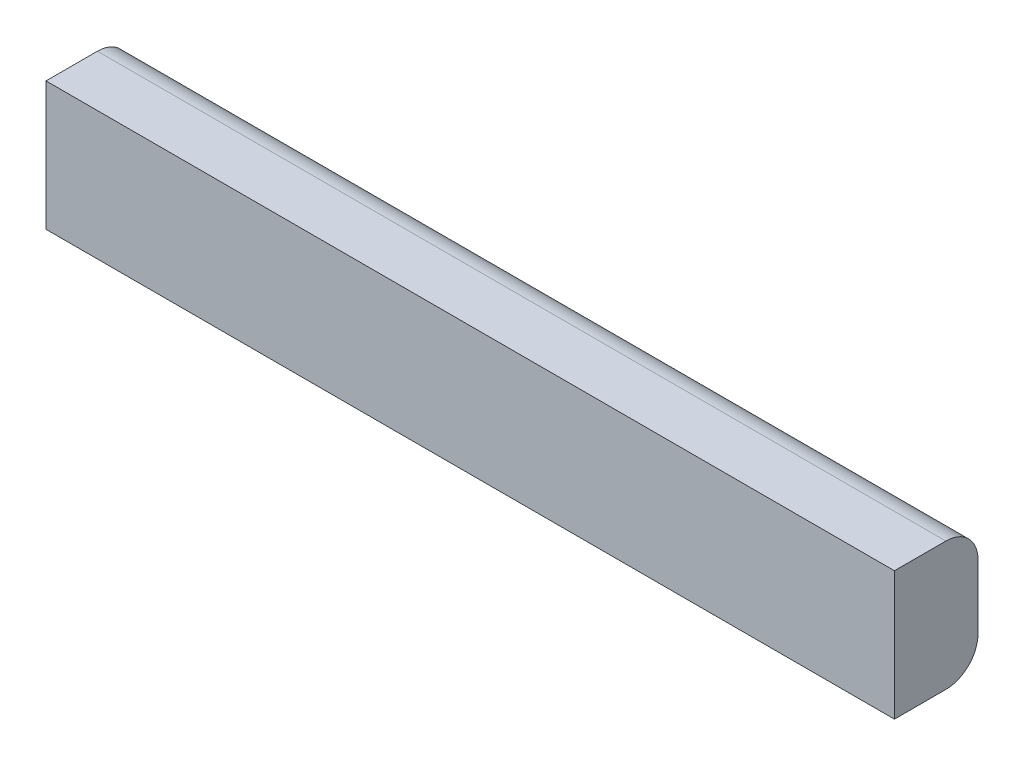
SolidWorks part; units mm, degrees
ref_plane "Front Plane" through (0, 0, 0) normal (0, 0, 1) x (1, 0, 0)
ref_plane "Top Plane" through (0, 0, 0) normal (0, 1, 0) x (1, 0, 0)
ref_plane "Right Plane" through (0, 0, 0) normal (1, 0, 0) x (0, 0, -1)
sketch "Sketch1" plane through (0, 0, 0) normal (1, 0, 0) x (0, 0, -1)
  line L1 (49.3736, 66.0217) -> (-1.4264, 66.0217)
  line L2 (81.1236, 34.2717) -> (81.1236, -29.2283)
  line L3 (49.3736, -60.9783) -> (-1.4264, -60.9783)
  line L4 (-1.4264, 66.0217) -> (-1.4264, -60.9783)
  arc A0 (49.3736, 66.0217) -> (81.1236, 34.2717) centre (49.3736, 34.2717) cw
  arc A1 (81.1236, -29.2283) -> (49.3736, -60.9783) centre (49.3736, -29.2283) cw
  point P8 (81.1236, -60.9783)
  dimension "D3" = 31.75
  dimension "D1" = 127
extrude "Boss-Extrude1" add sketch "Sketch1" along normal mid plane 838.2
equation "\"bumple\"= 24in'bumpler length"
equation "\"D1@Boss-Extrude1\"=\"bumple\""
